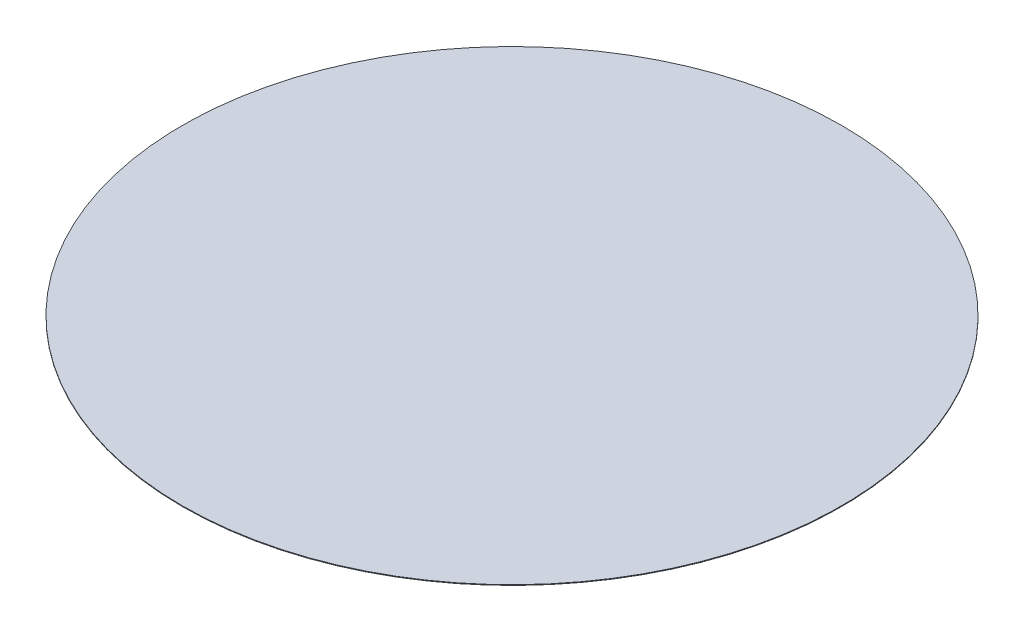
SolidWorks part; units mm, degrees
material "Thornel VCB-20 Carbon Cloth"
ref_plane "Front Plane" through (0, 0, 0) normal (0, 0, 1) x (1, 0, 0)
ref_plane "Top Plane" through (0, 0, 0) normal (0, 1, 0) x (1, 0, 0)
ref_plane "Right Plane" through (0, 0, 0) normal (1, 0, 0) x (0, 0, -1)
sketch "Sketch1" plane through (0, 0, 0) normal (0, 1, 0) x (1, 0, 0)
  circle A0 centre (0, 0) radius 2440
  dimension "D1" = 4880
extrude "Boss-Extrude1" add sketch "Sketch1" along normal blind 5 contours A0
